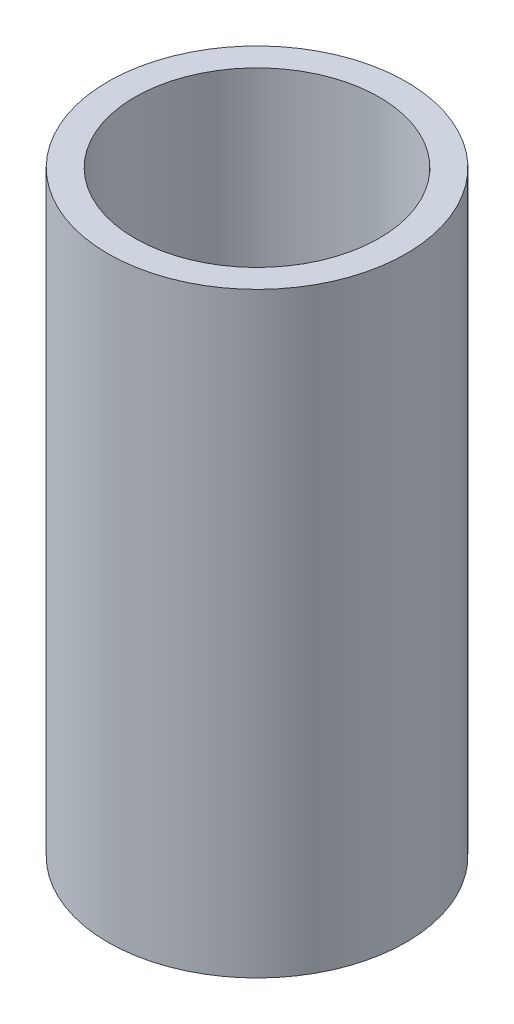
SolidWorks part; units mm, degrees
ref_plane "Front Plane" through (0, 0, 0) normal (0, 0, 1) x (1, 0, 0)
ref_plane "Top Plane" through (0, 0, 0) normal (0, 1, 0) x (1, 0, 0)
ref_plane "Right Plane" through (0, 0, 0) normal (1, 0, 0) x (0, 0, -1)
sketch "Sketch1" plane through (0, 0, 0) normal (0, 1, 0) x (1, 0, 0)
  circle A0 centre (0, 0) radius 12.7
  circle A1 centre (0, 0) radius 10.414
  dimension "D1" = 25.4
  dimension "D2" = 20.828
extrude "Boss-Extrude1" add sketch "Sketch1" along normal blind 50.8
